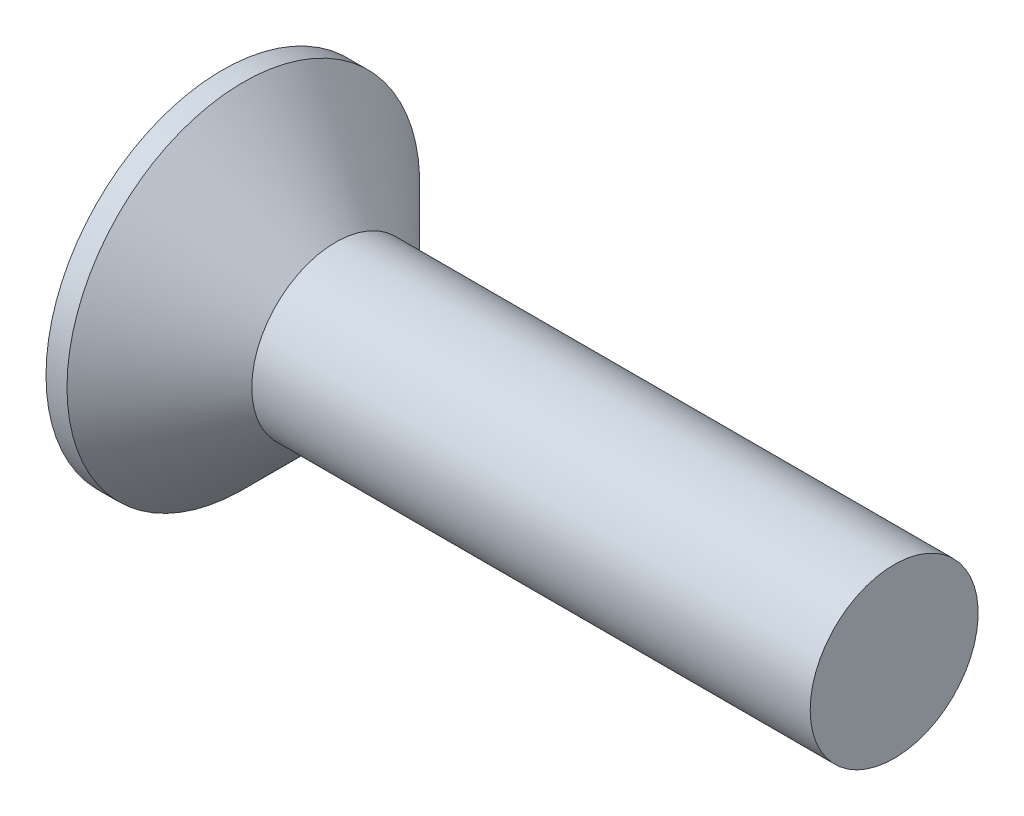
SolidWorks part; units mm, degrees
revolve "Base-Revolve" add sketch "BodySke" angle 360 about L5
sketch "BodySke" plane through (0, 0, 0) normal (0, 0, 1) x (1, 0, 0)
  line L0 (0, 0) -> (0, 4.2)
  line L1 (0, 4.2) -> (0.5, 4.2)
  line L2 (2.7, 2) -> (16, 2)
  line L3 (16, 2) -> (16, 0)
  line L4 (16, 0) -> (0, 0)
  line L5 (-6.35, 0) -> (82.55, 0) construction
  line L6 (2.7, -2) -> (16, -2) construction
  line L7 (0.5, -4.2) -> (2.7, -2) construction
  line L8 (0.5, 4.2) -> (2.7, 2)
  line L9 (0, -4.2) -> (0.5, -4.2) construction
  line L10 (3.4, 3.5875) -> (3.4, -5.9375) construction
  line L11 (0, 6.35) -> (0, -3.175) construction
  dimension "Diameter" = 4
  dimension "Length" = 16
  dimension "Head_ht" = 2.7
  dimension "Head_dia" = 8.4
  dimension "Head_ang" = 90
  dimension "D6" = 0.5
  dimension "Advance" = 0.7
  dimension "Thread_nom" = 16
cosmetic thread "ThreadCosmetic" parameters "Thread_length"=12.6, "Thread_minor"=3.22
extrude "Slot" [suppressed] cut sketch "Sketch2" against normal blind 1.3
sketch "Sketch2" plane through (0, 0, 0) normal (-1, 0, 0) x (0, 0, 1)
  line L0 (-4.2, -0.75) -> (4.2, -0.75)
  line L1 (-4.2, -0.75) -> (-4.2, 0.75)
  line L2 (4.2, 0.75) -> (-4.2, 0.75)
  line L3 (4.2, 0.75) -> (4.2, -0.75)
  dimension "Slot_width" = 1.5
  dimension "D1" = 0.75
  dimension "D2" = 8.4
  dimension "D3" = 4.2
ref_plane "Plane1" through (0, 0, 0) normal (0, 0, 1) x (1, 0, 0)
ref_plane "Plane2" through (0, 0, 0) normal (0, 1, 0) x (1, 0, 0)
ref_plane "Plane3" through (0, 0, 0) normal (1, 0, 0) x (0, 0, -1)
sketch "Sketch3" plane through (0, 0, 0) normal (-1, 0, 0) x (0, 0, 1)
  line L0 (-0.48, 2.23) -> (0.48, 2.23)
  line L1 (0.48, 2.23) -> (0.48, -2.23)
  line L2 (0.48, -2.23) -> (-0.48, -2.23)
  line L3 (-0.48, -2.23) -> (-0.48, 2.23)
  dimension "Cross_dia" = 4.46
  dimension "Cross_width" = 0.96
  dimension "D1" = 2.23
  dimension "D2" = 0.48
ref_plane "Plane4" through (2.65, 0, 0) normal (-1, 0, 0) x (0, 0, 1)
sketch "Sketch4" plane through (2.65, 0, 0) normal (-1, 0, 0) x (0, 0, 1)
  line L0 (-0.24, 0.24) -> (0.24, 0.24)
  line L3 (0.24, 0.24) -> (0.24, -0.24)
  line L4 (0.24, -0.24) -> (-0.24, -0.24)
  line L5 (-0.24, -0.24) -> (-0.24, 0.24)
  dimension "D2" = 0.48
  dimension "D1" = 0.48
  dimension "D3" = 0.24
  dimension "D4" = 0.24
loft "Cross" cut profiles "Sketch3", "Sketch4"
pattern_circular "CirPattern1" count 2 every 90 about axis through (0, 0, 0) along (1, 0, 0) of "Cross"
sketch "ThdSchSke" plane through (0, 0, 0) normal (0, 0, 1) x (1, 0, 0)
  line L0 (3.4, -1.61) -> (3.1269, -2)
  line L1 (3.4, -1.61) -> (3.6731, -2)
  line L2 (3.6731, -2) -> (3.6731, -2.5)
  line L3 (-3.175, 0) -> (5.1513, 0) construction
  line L5 (3.6731, -2.5) -> (3.1269, -2.5)
  line L6 (3.1269, -2.5) -> (3.1269, -2)
  line L7 (0, 4.2) -> (0, -4.2) construction
  dimension "Diameter" = 4
  dimension "Thread_minor" = 3.22
  dimension "Start" = 3.4
revolve "ThreadSchematic" [suppressed] cut sketch "ThdSchSke" angle 360 about L3
pattern_linear "ThdSchPat" [suppressed]
equation "\"D1@Sketch3\" = \"Cross_dia@Sketch3\" / 2"
equation "\"D2@Sketch3\" = \"Cross_width@Sketch3\" / 2"
equation "\"D1@Sketch4\" = \"Cross_width@Sketch3\" *.5"
equation "\"D2@Sketch4\" = \"D1@Sketch4\""
equation "\"D4@Sketch4\" = \"D2@Sketch4\" / 2"
equation "\"D3@Sketch4\" = \"D1@Sketch4\" / 2"
equation "\"D1@Sketch2\" = \"Slot_width@Sketch2\" / 2"
equation "\"D2@Sketch2\" = \"Head_dia@BodySke\""
equation "\"D3@Sketch2\" = \"D2@Sketch2\" / 2"
equation "\"Thread_length@ThreadCosmetic\" = ((sgn( (\"Length@BodySke\" - \"Advance@BodySke\" - \"Head_ht@BodySke\" ) - \"Thread_nom@BodySke\" )-1)*( (\"Length@BodySke\" - \"Advance@BodySke\" - \"Head_ht@BodySke\" ) - \"Thread_nom@BodySke\" ))/-2+ \"Thread_nom@BodySke\""
equation "\"Thread_minor@ThdSchSke\" = \"Thread_minor@ThreadCosmetic\""
equation "\"Diameter@ThdSchSke\" = \"Diameter@BodySke\""
equation "\"Overcut@ThdSchSke\" = \"Diameter@BodySke\" * 1.25"
equation "\"Start@ThdSchSke\" = 0.000001 + \"Length@BodySke\" - \"Thread_length@ThreadCosmetic\"  '---Countersunk---"
equation "\"Num_threads@ThdSchPat\" = int( \"Thread_length@ThreadCosmetic\" / \"Advance@BodySke\" + 0.999 )  + 1"
equation "\"Advance@ThdSchPat\" = \"Thread_length@ThreadCosmetic\" /  (\"Num_threads@ThdSchPat\" - 1) 'relax it"
